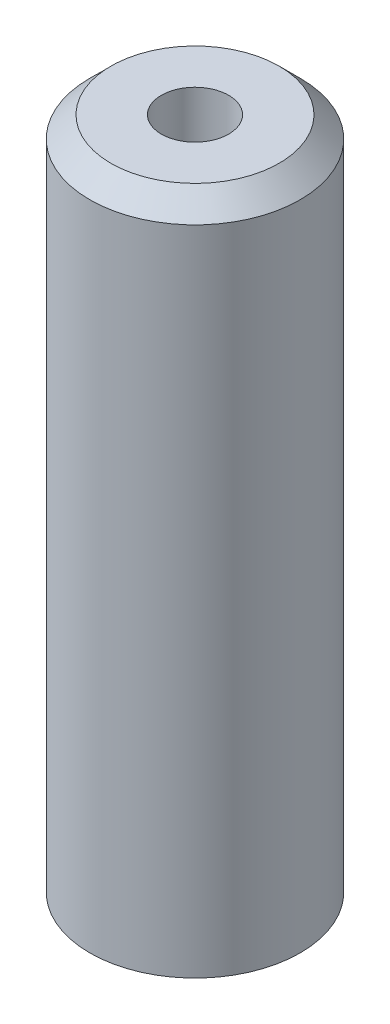
SolidWorks part; units mm, degrees
ref_plane "Plan de face" through (0, 0, 0) normal (0, 0, 1) x (1, 0, 0)
ref_plane "Plan de dessus" through (0, 0, 0) normal (0, 1, 0) x (1, 0, 0)
ref_plane "Plan de droite" through (0, 0, 0) normal (1, 0, 0) x (0, 0, -1)
sketch "Esquisse1" plane through (0, 0, 0) normal (0, 1, 0) x (1, 0, 0)
  circle A0 centre (0, 0) radius 2.5
  dimension "D1" = 5
extrude "Boss.-Extru.1" add sketch "Esquisse1" along normal blind 6 and the other way blind 10
hole_wizard "Trou taraudé M21" positions "Esquisse2" profile "Esquisse3" tap size "M2" standard "ISO"
sketch "Esquisse2" plane through (0, 6, 0) normal (0, 1, 0) x (1, 0, 0)
  point P0 (0, 0)
sketch "Esquisse3" plane through (0, 6, 0) normal (1, 0, 0) x (0, 0, 1)
  line L0 (0, 0) -> (0, 6.4807)
  line L1 (0, 6.4807) -> (0.8, 6)
  line L2 (0.8, 6) -> (0.8, 0)
  line L5 (0.8, 0) -> (0, 0)
  line L10 (0, 6.4807) -> (-0.8, 6) construction
  line L11 (0, -6.35) -> (0, 107.95) construction
  dimension "Diamètre du trou pour taraudage" = 1.6
  dimension "Profondeur du trou pour taraudage" = 6
  dimension "Angle de pointe" = 118
cosmetic thread "Filetage de perçage1" parameters "D1"=4, "D2"=2
chamfer "Chanfrein1" distance 0.5 angle 45 1 edges at (0, 6, 2.5)
